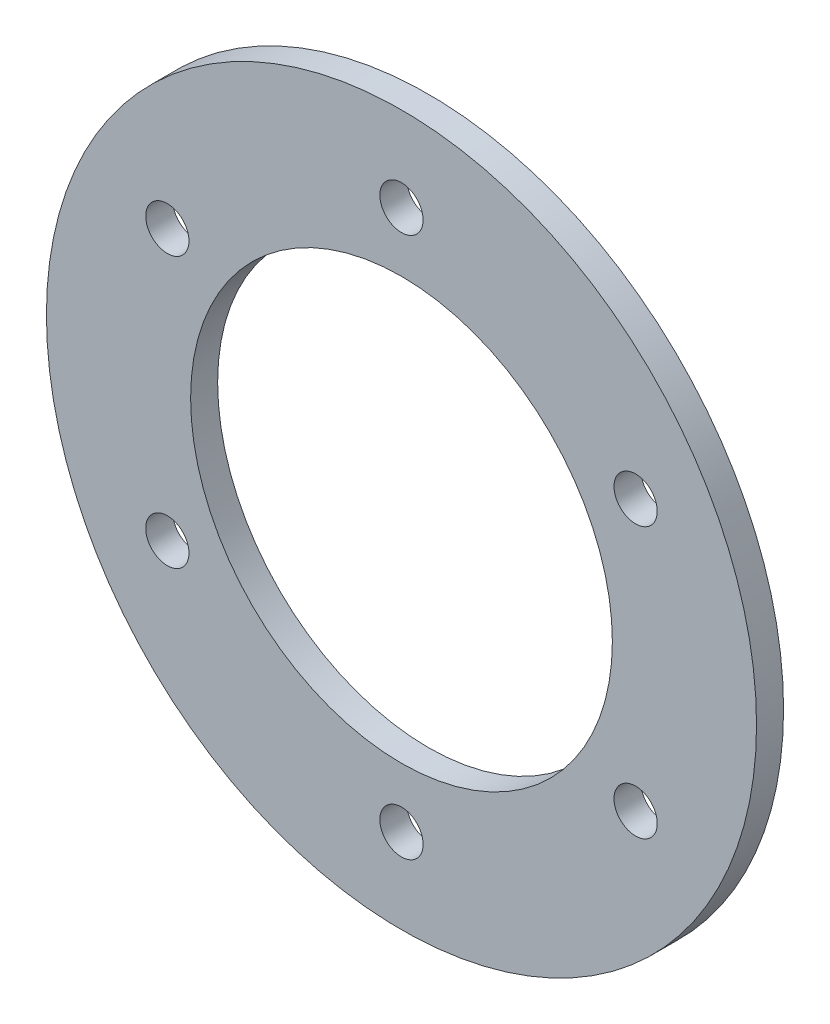
SolidWorks part; units mm, degrees
ref_plane "Front Plane" through (0, 0, 0) normal (0, 0, 1) x (1, 0, 0)
ref_plane "Top Plane" through (0, 0, 0) normal (0, 1, 0) x (1, 0, 0)
ref_plane "Right Plane" through (0, 0, 0) normal (1, 0, 0) x (0, 0, -1)
sketch "Sketch1" plane through (0, 0, 0) normal (0, 0, 1) x (1, 0, 0)
  circle A0 centre (0, 0) radius 11.7
  circle A1 centre (0, 0) radius 19.7
  dimension "D1" = 23.4
  dimension "D2" = 8
extrude "Boss-Extrude1" add sketch "Sketch1" along normal mid plane 1.5
hole_wizard "M2 Clearance Hole1" positions "Sketch2" profile "Sketch3" hole size "M2" standard "ANSI Metric" end condition up to next
sketch "Sketch2" plane through (0, 0, 0.75) normal (0, 0, 1) x (1, 0, 0)
  circle A3 centre (0, 0) radius 15
  point P76 (0, 15)
  point P83 (12.9904, 7.5)
  point P84 (12.9904, -7.5)
  point P85 (0, -15)
  point P86 (-12.9904, -7.5)
  point P87 (-12.9904, 7.5)
  dimension "D1" = 30
sketch "Sketch3" plane through (-12.9904, 7.5, 0.75) normal (1, 0, 0) x (0, -1, 0)
  line L0 (0, 0) -> (0, 1.5)
  line L1 (0, 1.5) -> (1.2, 1.5)
  line L2 (1.2, 1.5) -> (1.2, 0)
  line L5 (1.2, 0) -> (0, 0)
  line L11 (0, -6.35) -> (0, 107.95) construction
  dimension "Thru Hole Dia." = 2.4
  dimension "Thru Hole Depth" = 1.5
